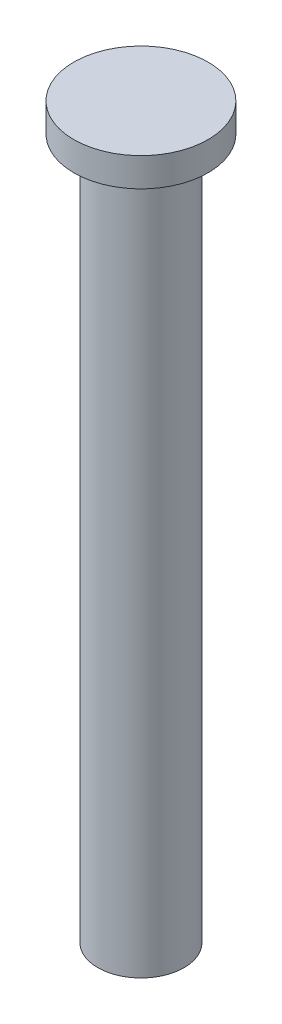
SolidWorks part; units mm, degrees
ref_plane "Front Plane" through (0, 0, 0) normal (0, 0, 1) x (1, 0, 0)
ref_plane "Top Plane" through (0, 0, 0) normal (0, 1, 0) x (1, 0, 0)
ref_plane "Right Plane" through (0, 0, 0) normal (1, 0, 0) x (0, 0, -1)
sketch "Sketch3" plane through (0, 0, 0) normal (0, 0, 1) x (1, 0, 0)
  line L0 (0, 314.5853) -> (0, -264.6322) construction
  line L1 (22.5, 0) -> (0, 0)
  line L2 (0, 0) -> (0, 380)
  line L3 (0, 380) -> (35, 380)
  line L4 (35, 380) -> (35, 365)
  line L5 (35, 365) -> (22.5, 365)
  line L6 (22.5, 365) -> (22.5, 0)
  dimension "D1" = 380
  dimension "D2" = 35
  dimension "D3" = 22.5
  dimension "D4" = 15
revolve "Revolve1" add sketch "Sketch3" angle 360 about L0
